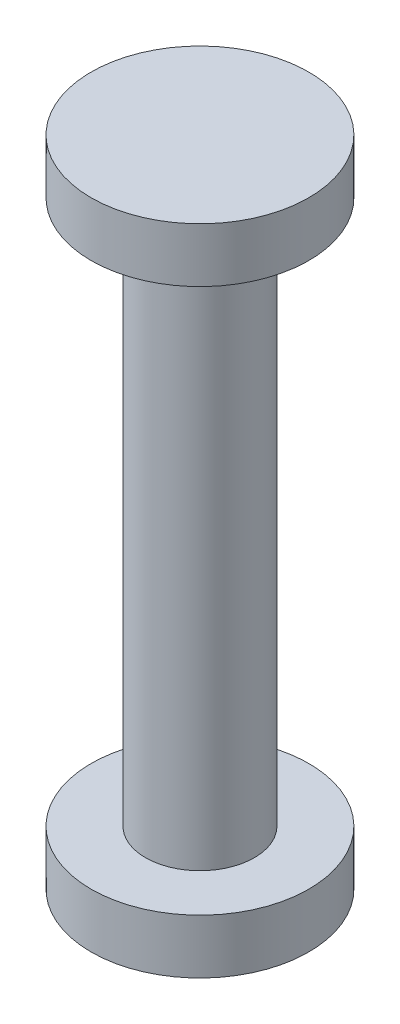
SolidWorks part; units mm, degrees
ref_plane "Front Plane" through (0, 0, 0) normal (0, 0, 1) x (1, 0, 0)
ref_plane "Top Plane" through (0, 0, 0) normal (0, 1, 0) x (1, 0, 0)
ref_plane "Right Plane" through (0, 0, 0) normal (1, 0, 0) x (0, 0, -1)
sketch "Sketch1" plane through (0, 0, 0) normal (0, 1, 0) x (1, 0, 0)
  circle A0 centre (0, 0) radius 5
  dimension "D1" = 10
extrude "Boss-Extrude1" add sketch "Sketch1" along normal mid plane 50
sketch "Sketch2" plane through (0, 25, 0) normal (0, 1, 0) x (1, 0, 0)
  circle A0 centre (0, 0) radius 10
  dimension "D1" = 20
extrude "Boss-Extrude2" add sketch "Sketch2" along normal blind 5
mirror "Mirror1" about plane through (0, 0, 0) normal (0, 1, 0) of "Boss-Extrude2"
